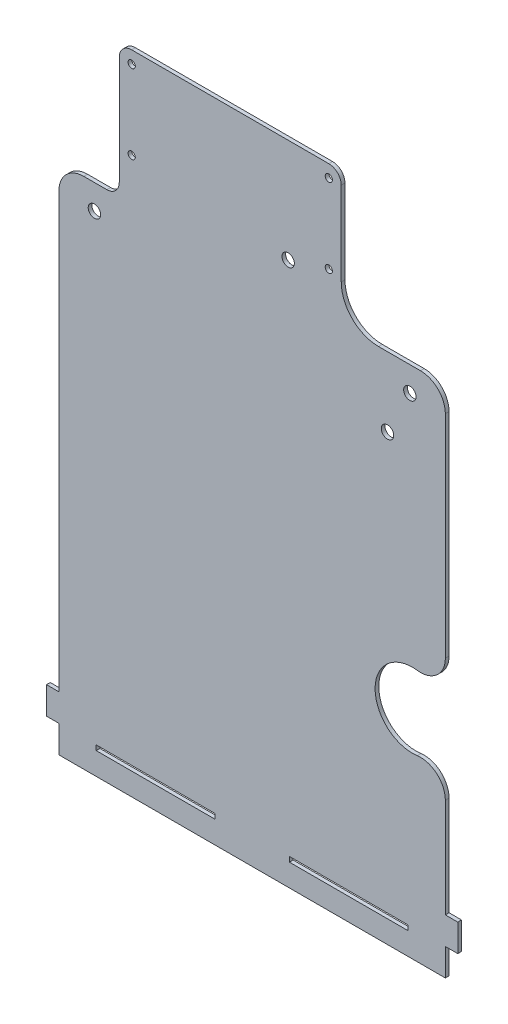
SolidWorks part; units mm, degrees
ref_plane "Front Plane" through (0, 0, 0) normal (0, 0, 1) x (1, 0, 0)
ref_plane "Top Plane" through (0, 0, 0) normal (0, 1, 0) x (1, 0, 0)
ref_plane "Right Plane" through (0, 0, 0) normal (1, 0, 0) x (0, 0, -1)
sketch "Sketch1" plane through (0, 0, 0) normal (0, 0, 1) x (1, 0, 0)
  line L0 (0, 11) -> (155.575, 11) construction
  line L1 (0, 0) -> (155.575, 0) construction
  line L2 (0, 0) -> (0, 190.5) construction
  line L3 (0, 190.5) -> (155.575, 190.5) construction
  line L4 (155.575, 0) -> (155.575, 68.7774) construction
  line L5 (14.2875, 185.7375) -> (141.2875, 185.7375) construction
  line L6 (14.2875, 185.7375) -> (14.2875, 4.7625) construction
  line L7 (14.2875, 4.7625) -> (141.2875, 4.7625) construction
  line L8 (141.2875, 185.7375) -> (141.2875, 4.7625) construction
  line L9 (0, 179.5) -> (155.575, 179.5) construction
  line L10 (24.2875, 244.4875) -> (24.2875, 200.7375)
  line L11 (29.2875, 212.7375) -> (108.6625, 212.7375) construction
  line L12 (29.2875, 212.7375) -> (29.2875, 244.4875) construction
  line L13 (29.2875, 244.4875) -> (108.6625, 244.4875) construction
  line L14 (108.6625, 212.7375) -> (108.6625, 244.4875) construction
  line L15 (19.2875, 195.7375) -> (10, 195.7375)
  line L16 (0, 185.7375) -> (0, 11)
  line L17 (0, 11) -> (-5, 11)
  line L18 (-5, 11) -> (-5, 0)
  line L19 (-5, 0) -> (0, 0)
  line L20 (0, 0) -> (0, -11)
  line L21 (0, -11) -> (155.575, -11)
  line L22 (155.575, -11) -> (155.575, 0)
  line L23 (155.575, 0) -> (160.575, 0)
  line L24 (160.575, 0) -> (160.575, 11)
  line L25 (160.575, 11) -> (155.575, 11)
  line L26 (155.575, 11) -> (155.575, 50.9546)
  line L27 (145.575, 195.7375) -> (128.6625, 195.7375)
  line L28 (113.6625, 210.7375) -> (113.6625, 244.4875)
  line L29 (108.6625, 249.4875) -> (29.2875, 249.4875)
  line L30 (155.575, 82.6976) -> (155.575, 190.5) construction
  line L31 (155.575, 100.5204) -> (155.575, 185.7375)
  circle A4 centre (141.2875, 4.7625) radius 2.5 construction
  circle A5 centre (14.2875, 4.7625) radius 2.5 construction
  circle A6 centre (14.2875, 185.7375) radius 2.5
  circle A7 centre (141.2875, 185.7375) radius 2.5
  circle A8 centre (108.6625, 212.7375) radius 1.45
  circle A9 centre (108.6625, 244.4875) radius 1.45
  circle A10 centre (29.2875, 244.4875) radius 1.45
  circle A11 centre (29.2875, 212.7375) radius 1.45
  circle A12 centre (132.2875, 207.7375) radius 5 construction
  circle A13 centre (142.2875, 75.7375) radius 4.75 construction
  circle A14 centre (141.2875, 158.7375) radius 2.5 construction
  circle A15 centre (132.2875, 207.7375) radius 7.5 construction
  arc A16 (128.6625, 195.7375) -> (113.6625, 210.7375) centre (128.6625, 210.7375) cw
  arc A17 (24.2875, 200.7375) -> (19.2875, 195.7375) centre (19.2875, 200.7375) cw
  arc A18 (24.2875, 244.4875) -> (29.2875, 249.4875) centre (29.2875, 244.4875) cw
  arc A19 (113.6625, 244.4875) -> (108.6625, 249.4875) centre (108.6625, 244.4875) ccw
  arc A20 (155.575, 185.7375) -> (145.575, 195.7375) centre (145.575, 185.7375) ccw
  arc A21 (10, 195.7375) -> (0, 185.7375) centre (10, 185.7375) ccw
  arc A22 (144.26, 90.6072) -> (144.26, 60.8678) centre (142.2875, 75.7375) ccw
  arc A23 (144.26, 60.8678) -> (155.575, 50.9546) centre (145.575, 50.9546) cw
  arc A24 (144.26, 90.6072) -> (155.575, 100.5204) centre (145.575, 100.5204) ccw
  circle A25 centre (132.2875, 167.7375) radius 2.5
  circle A26 centre (92.2875, 207.7375) radius 2.5
  point P13 (14.2875, 95.25)
  point P14 (0, 95.25)
  point P15 (77.7875, 4.7625)
  point P16 (77.7875, 0)
  point P72 (0, 0)
  point P73 (0, 0)
  dimension "D3" = 5
  dimension "D4" = 5
  dimension "D5" = 5
  dimension "D6" = 5
  dimension "D13" = 2.9
  dimension "D18" = 10
  dimension "D19" = 9.5
  dimension "D20" = 5
  dimension "D24" = 15
  dimension "D33" = 15
  dimension "D34" = 5
  dimension "D35" = 10
  dimension "D36" = 10
  dimension "D37" = 5
  dimension "D38" = 5
  dimension "D1" = 190.5
  dimension "D2" = 155.575
  dimension "D7" = 127
  dimension "D8" = 180.975
  dimension "D9" = 11
  dimension "D10" = 11
  dimension "D11" = 79.375
  dimension "D12" = 31.75
  dimension "D14" = 10
  dimension "D15" = 132
  dimension "D16" = 1
  dimension "D17" = 49
  dimension "D21" = 27
  dimension "D22" = 27
  dimension "D23" = 15
  dimension "D25" = 10
  dimension "D26" = 5
  dimension "D27" = 5
  dimension "D28" = 5
  dimension "D29" = 10
  dimension "D30" = 11
  dimension "D31" = 5
  dimension "D32" = 5
  dimension "D39" = 40
  dimension "D40" = 40
extrude "Boss-Extrude1" add sketch "Sketch1" along normal blind 1.5
sketch "Sketch2" plane through (0, 0, 1.5) normal (0, 0, 1) x (1, 0, 0)
  line L0 (0, 0) -> (155.575, 0) construction
  line L1 (0, -2) -> (155.575, -2) construction
  line L2 (0, 0) -> (0, -11) construction
  line L3 (155.575, -11) -> (155.575, 0) construction
  line L4 (15, -2) -> (62.7875, -2)
  line L5 (92.7875, -2) -> (140.575, -2)
  line L7 (15, -2) -> (62.7875, -2)
  line L8 (15, -2) -> (15, 0)
  line L9 (15, 0) -> (62.7875, 0)
  line L10 (62.7875, -2) -> (62.7875, 0)
  line L11 (92.7875, -2) -> (140.575, -2)
  line L12 (92.7875, -2) -> (92.7875, 0)
  line L13 (92.7875, 0) -> (140.575, 0)
  line L14 (140.575, -2) -> (140.575, 0)
  point P18 (140.575, 0)
  dimension "D1" = 2
  dimension "D2" = 15
  dimension "D3" = 30
  dimension "D4" = 15
extrude "Cut-Extrude1" cut sketch "Sketch2" against normal through all contours L4 L10 L9 L8 | L5 L14 L13 L12
